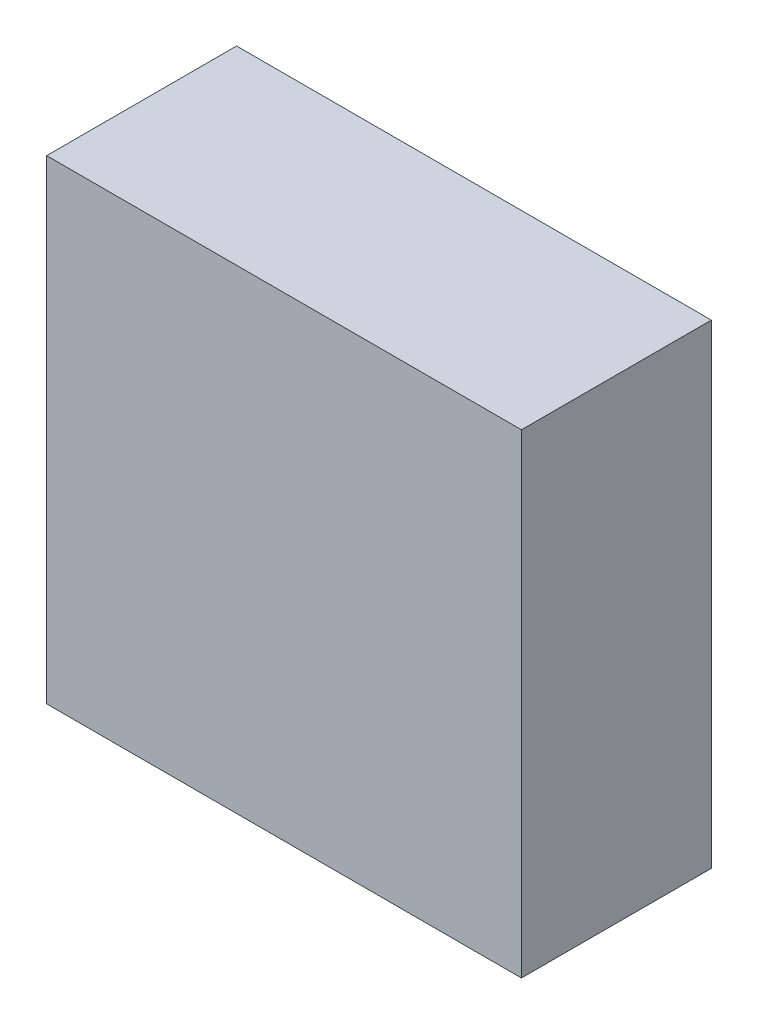
SolidWorks part; units mm, degrees
ref_plane "Front Plane" through (0, 0, 0) normal (0, 0, 1) x (1, 0, 0)
ref_plane "Top Plane" through (0, 0, 0) normal (0, 1, 0) x (1, 0, 0)
ref_plane "Right Plane" through (0, 0, 0) normal (1, 0, 0) x (0, 0, -1)
sketch "Sketch1" plane through (0, 0, 0) normal (0, 0, 1) x (1, 0, 0)
  line L0 (-5.55, 5.55) -> (-1.5, 5.55)
  line L1 (-7.5, -7.5) -> (7.5, -7.5)
  line L2 (-7.5, -7.5) -> (-7.5, 7.5)
  line L3 (-7.5, 7.5) -> (7.5, 7.5)
  line L4 (7.5, -7.5) -> (7.5, 7.5)
  line L5 (-7.5, -7.5) -> (7.5, 7.5) construction
  line L6 (-7.5, 7.5) -> (7.5, -7.5) construction
  line L7 (-5.55, 5.55) -> (-5.55, 1.5)
  line L8 (-5.55, 1.5) -> (-3.55, 1.5)
  line L9 (-3.55, 1.5) -> (-3.55, -1.5)
  line L10 (-1.5, 5.55) -> (-1.5, 3.55)
  line L11 (-1.5, 3.55) -> (1.5, 3.55)
  line L12 (1.5, 3.55) -> (1.5, 5.55)
  line L13 (1.5, 5.55) -> (5.55, 5.55)
  line L14 (-3.55, -1.5) -> (-5.55, -1.5)
  line L15 (-5.55, -1.5) -> (-5.55, -5.55)
  line L16 (-5.55, -5.55) -> (-1.5, -5.55)
  line L17 (-1.5, -5.55) -> (-1.5, -3.55)
  line L18 (-1.5, -3.55) -> (1.5, -3.55)
  line L19 (1.5, -3.55) -> (1.5, -5.55)
  line L20 (1.5, -5.55) -> (5.55, -5.55)
  line L21 (5.55, -5.55) -> (5.55, -1.5)
  line L22 (5.55, -1.5) -> (3.55, -1.5)
  line L23 (3.55, -1.5) -> (3.55, 1.5)
  line L24 (3.55, 1.5) -> (5.55, 1.5)
  line L25 (5.55, 5.55) -> (5.55, 1.5)
  point P0 (0, 0)
  point P26 (0, 0)
  point P28 (6.1734, 6.1734)
  dimension "D1" = 15
  dimension "D2" = 15
  dimension "D3" = 4.05
  dimension "D4" = 3
  dimension "D5" = 2
extrude "Boss-Extrude1" add sketch "Sketch1" along normal blind 5
sketch "Sketch2" plane through (0, 0, 5) normal (0, 0, 1) x (1, 0, 0)
  line L0 (7.5, -7.5) -> (7.5, 7.5) construction
  line L1 (-7.5, 7.5) -> (7.5, 7.5)
  line L2 (-7.5, 7.5) -> (-7.5, -7.5)
  line L3 (-7.5, -7.5) -> (7.5, -7.5)
  line L4 (7.5, 7.5) -> (7.5, -7.5)
extrude "Boss-Extrude2" add sketch "Sketch2" along normal blind 1
